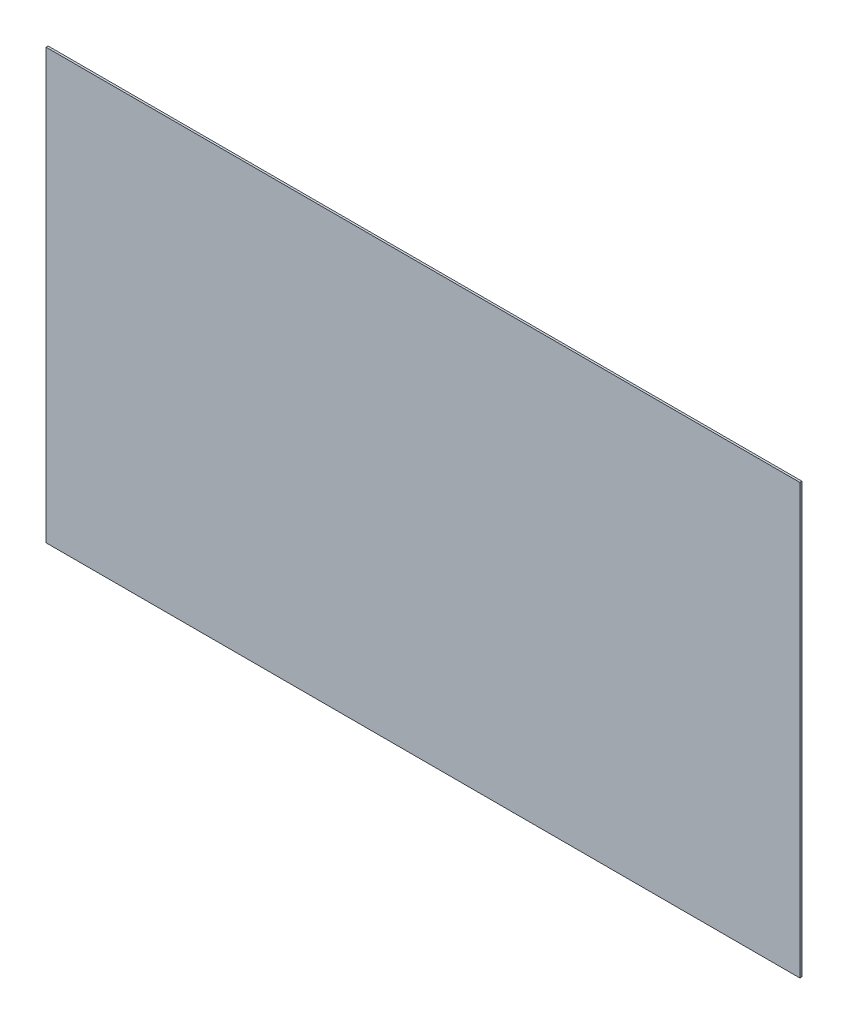
SolidWorks part; units mm, degrees
ref_plane "Front Plane" through (0, 0, 0) normal (0, 0, 1) x (1, 0, 0)
ref_plane "Top Plane" through (0, 0, 0) normal (0, 1, 0) x (1, 0, 0)
ref_plane "Right Plane" through (0, 0, 0) normal (1, 0, 0) x (0, 0, -1)
sketch "Sketch1" plane through (0, 0, 0) normal (0, 0, 1) x (1, 0, 0)
  line L1 (0, 0) -> (720, 0)
  line L2 (0, 0) -> (0, 410)
  line L3 (0, 410) -> (720, 410)
  line L4 (720, 0) -> (720, 410)
  dimension "D1" = 720
  dimension "D2" = 410
extrude "Boss-Extrude1" add sketch "Sketch1" along normal blind 2
